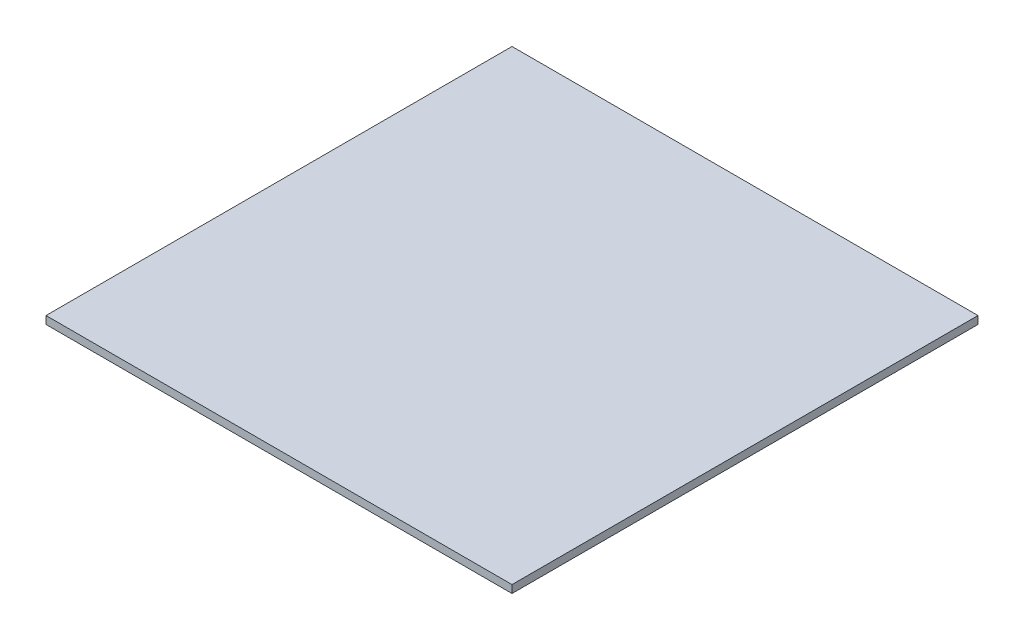
SolidWorks part; units mm, degrees
ref_plane "Спереди" through (0, 0, 0) normal (0, 0, 1) x (1, 0, 0)
ref_plane "Сверху" through (0, 0, 0) normal (0, 1, 0) x (1, 0, 0)
ref_plane "Справа" through (0, 0, 0) normal (1, 0, 0) x (0, 0, -1)
sketch "Эскиз1" plane through (0, 0, 0) normal (0, 1, 0) x (1, 0, 0)
  line L1 (0, 0) -> (300, 0)
  line L2 (0, 0) -> (0, -300)
  line L3 (0, -300) -> (300, -300)
  line L4 (300, 0) -> (300, -300)
extrude "Бобышка-Вытянуть1" add sketch "Эскиз1" along normal blind 5
